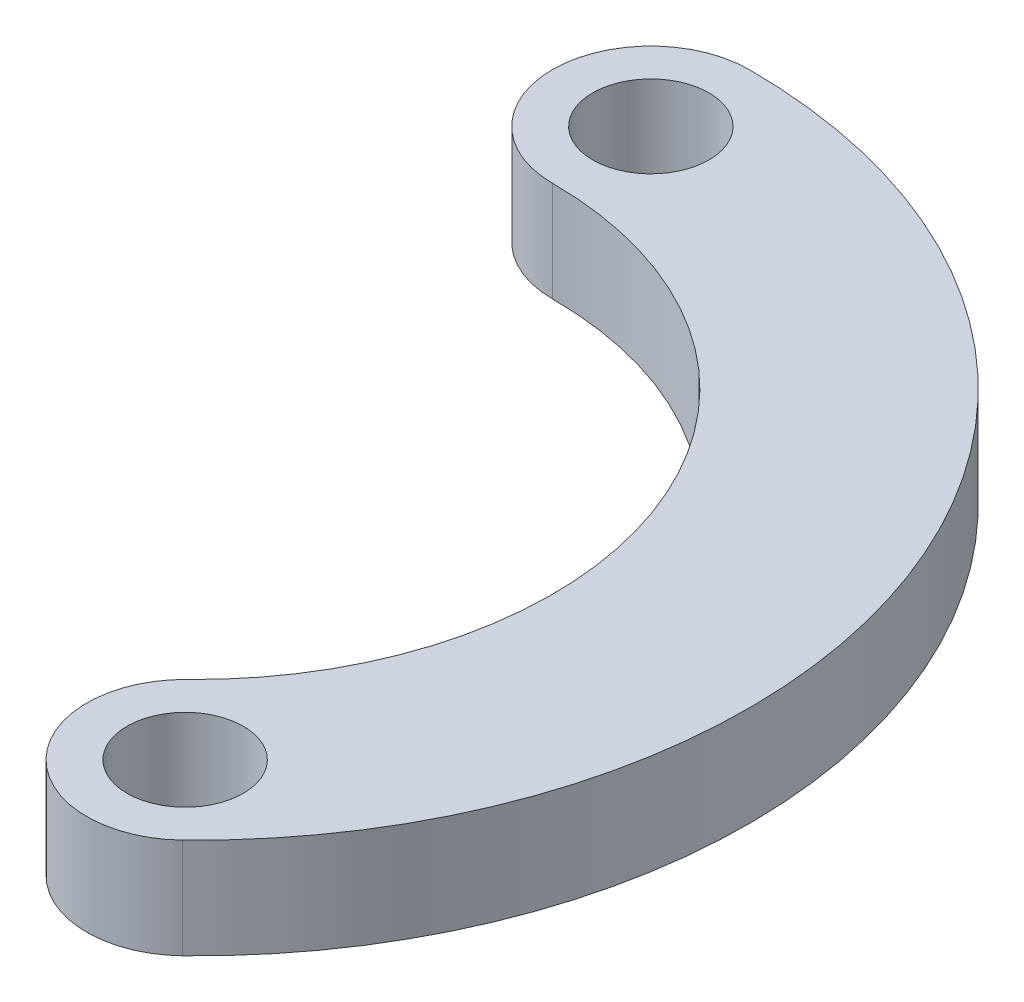
SolidWorks part; units mm, degrees
ref_plane "Piano frontale" through (0, 0, 0) normal (0, 0, 1) x (1, 0, 0)
ref_plane "Piano superiore" through (0, 0, 0) normal (0, 1, 0) x (1, 0, 0)
ref_plane "Piano destro" through (0, 0, 0) normal (1, 0, 0) x (0, 0, -1)
sketch "Schizzo1" plane through (0, 0, 0) normal (0, 1, 0) x (1, 0, 0)
  line L0 (0, 0) -> (0, 12.1832)
  line L1 (0, 17.6676) -> (0, 0)
  line L2 (0, 0) -> (6.9119, -7.1574)
  line L3 (10.7325, -11.1138) -> (12.8339, -13.2899)
  circle A0 centre (0, 0) radius 15.45
  circle A2 centre (0, 0) radius 9.95
  arc A3 (0, 15.45) -> (0, 9.95) centre (0, 12.7) ccw
  arc A4 (6.9119, -7.1574) -> (10.7325, -11.1138) centre (8.8222, -9.1356) ccw
  dimension "D1" = 30.9
  dimension "D3" = 19.9
  dimension "D4" = 136
extrude "Estrusione-Estrusione1" add sketch "Schizzo1" against normal blind 2.8 contours A2 A4 A0 L1 | L1 A3
sketch "Schizzo3" plane through (0, 0, 0) normal (0, 1, 0) x (1, 0, 0)
  circle A0 centre (0, 12.7) radius 1.625
  circle A2 centre (8.8222, -9.1356) radius 1.625
  dimension "D1" = 3.25
  dimension "D2" = 3.25
extrude "Taglio-Estrusione1" cut sketch "Schizzo3" against normal through all
